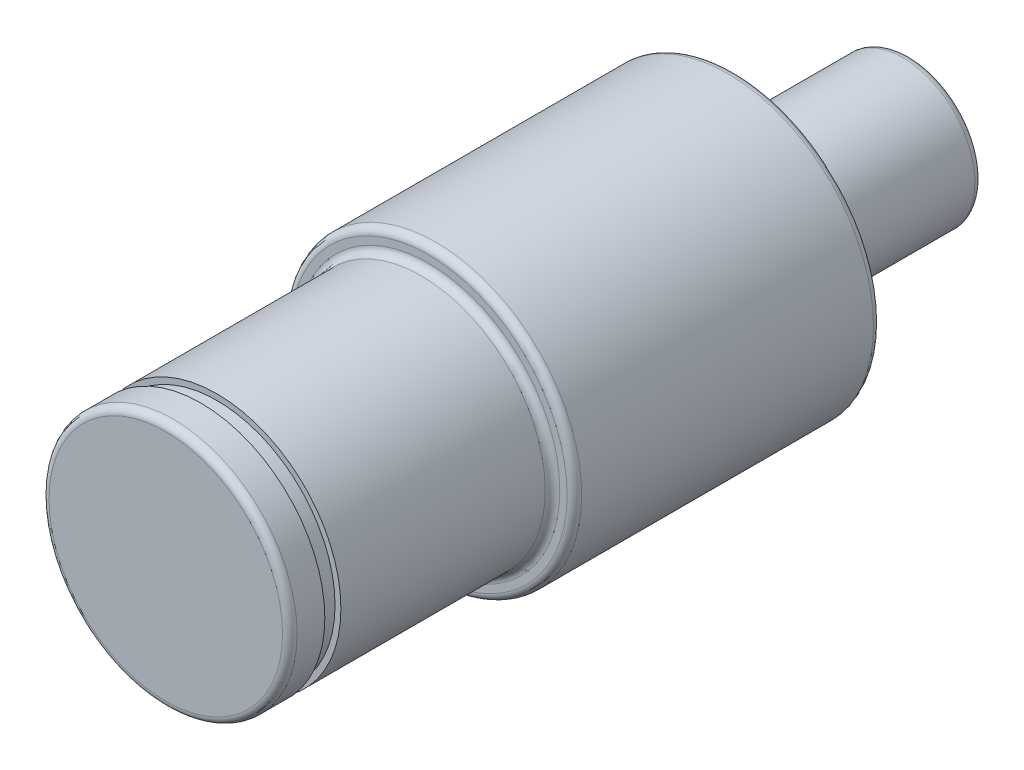
SolidWorks part; units mm, degrees
material "普通碳钢"
ref_plane "Front" through (0, 0, 0) normal (0, 0, 1) x (1, 0, 0)
ref_plane "Top" through (0, 0, 0) normal (0, 1, 0) x (1, 0, 0)
ref_plane "Right" through (0, 0, 0) normal (1, 0, 0) x (0, 0, -1)
sketch "草图1" plane through (0, 0, 0) normal (0, 0, 1) x (1, 0, 0)
  circle A0 centre (0, 0) radius 10
  dimension "D1" = 20
extrude "凸台-拉伸1" add sketch "草图1" along normal blind 21
sketch "草图2" plane through (0, 0, 21) normal (0, 0, 1) x (1, 0, 0)
  circle A0 centre (0, 0) radius 8.5
  dimension "D1" = 17
extrude "凸台-拉伸2" add sketch "草图2" along normal blind 18
sketch "草图3" plane through (0, 0, 0) normal (0, 0, -1) x (-1, 0, 0)
  circle A0 centre (0, 0) radius 4.95
  dimension "D1" = 9.9
extrude "凸台-拉伸3" add sketch "草图3" along normal blind 12
fillet "圆角1" radius 0.5 2 edges at (8.5, 0, 21) (-4.95, 0, 0)
fillet "圆角2" radius 0.5 4 edges at (10, 0, 0) (10, 0, 21) (8.5, 0, 39) (-4.95, 0, -12)
ref_plane "基准面1" through (0, 0, 35.5) normal (0, 0, 1) x (1, 0, 0)
sketch "草图4" plane through (0, 0, 35.5) normal (0, 0, 1) x (1, 0, 0)
  circle A0 centre (0, 0) radius 8.1
  dimension "D1" = 16.2
extrude "切除-拉伸1" cut sketch "草图4" along normal blind 1.1 flip side to cut
